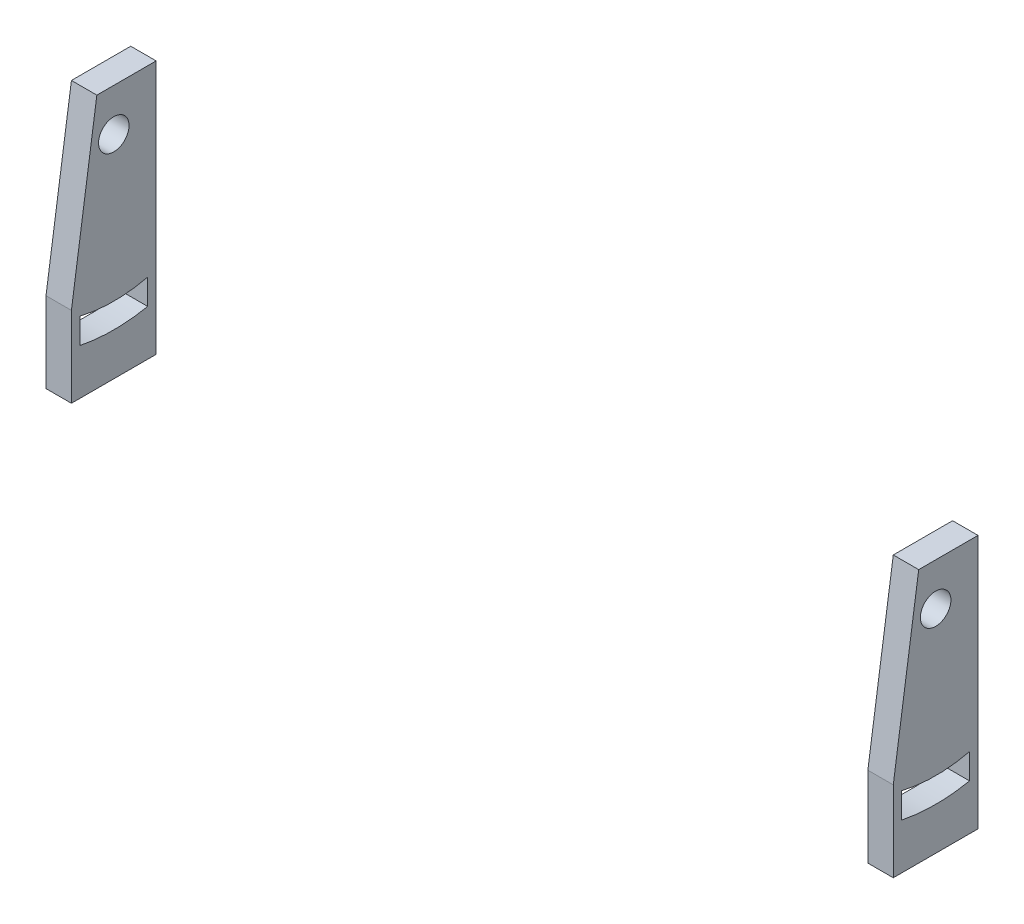
SolidWorks part; units mm, degrees
ref_plane "Front Plane" through (0, 0, 0) normal (0, 0, 1) x (1, 0, 0)
ref_plane "Top Plane" through (0, 0, 0) normal (0, 1, 0) x (1, 0, 0)
ref_plane "Right Plane" through (0, 0, 0) normal (1, 0, 0) x (0, 0, -1)
sketch "Sketch1" plane through (0, 0, 0) normal (1, 0, 0) x (0, 0, -1)
  line L1 (-11.9084, 16.5321) -> (-1.9084, 16.5321)
  line L2 (-11.9084, 16.5321) -> (-11.9084, -13.4679)
  line L3 (-11.9084, -13.4679) -> (-1.9084, -13.4679)
  line L4 (-1.9084, 16.5321) -> (-1.9084, -13.4679)
  dimension "D1" = 30
  dimension "D2" = 10
extrude "Boss-Extrude1" add sketch "Sketch1" along normal blind 100
sketch "Sketch2" plane through (0, 16.5321, 0) normal (0, 1, 0) x (1, 0, 0)
  line L0 (100, -11.9084) -> (0, -11.9084) construction
  line L1 (3, -11.9084) -> (97, -11.9084)
  line L2 (3, -11.9084) -> (3, -1.9084)
  line L3 (3, -1.9084) -> (97, -1.9084)
  line L4 (97, -11.9084) -> (97, -1.9084)
  line L5 (100, -1.9084) -> (0, -1.9084) construction
  dimension "D1" = 3
  dimension "D2" = 3
extrude "Cut-Extrude1" cut sketch "Sketch2" against normal blind 100
sketch "Sketch3" plane through (100, 0, 0) normal (1, 0, 0) x (0, 0, -1)
  line L0 (-1.9084, -13.4679) -> (-1.9084, 16.5321) construction
  line L2 (-11.9084, 16.5321) -> (-11.9084, -13.4679) construction
  line L3 (-1.9084, 16.5321) -> (-11.9084, 16.5321) construction
  circle A0 centre (-6.9084, 11.5321) radius 1.8
  point P4 (-6.9084, 16.5321)
  point P6 (-11.9084, 9.46)
  dimension "D1" = 5
  dimension "D2" = 5
  dimension "D3" = 5
extrude "Cut-Extrude2" cut sketch "Sketch3" against normal blind 100
sketch "Sketch4" plane through (100, 0, 0) normal (1, 0, 0) x (0, 0, -1)
  line L0 (-11.9084, 16.5321) -> (-11.9084, -13.4679) construction
  line L1 (-1.9084, -13.4679) -> (-1.9084, 16.5321) construction
  line L2 (-10.9084, -5.0638) -> (-10.9084, -8.0638)
  line L3 (-2.9109, -5.0644) -> (-2.9084, -8.0638)
  arc A0 (-2.9084, -8.0638) -> (-10.9084, -8.0638) centre (-6.9084, 11.5321) cw
  arc A1 (-2.9109, -5.0644) -> (-10.9084, -5.0638) centre (-6.9084, 11.5321) cw
  dimension "D3" = 20
  dimension "D1" = 1
  dimension "D2" = 1
  dimension "D4" = 1
  dimension "D5" = 1.0024
  dimension "D6" = 3
extrude "Cut-Extrude3" cut sketch "Sketch4" against normal blind 100
sketch "Sketch5" plane through (0, 0, 0) normal (-1, 0, 0) x (0, 0, 1)
  line L0 (8.9084, 16.5321) -> (11.9084, -3.9679)
  line L3 (1.9084, 16.5321) -> (11.9084, 16.5321) construction
  line L4 (11.9084, 16.5321) -> (11.9084, -13.4679) construction
  line L6 (8.9084, 16.5321) -> (11.9084, 16.5321)
  line L9 (11.9084, 16.5321) -> (11.9084, -3.9679)
  dimension "D1" = 3
  dimension "D2" = 9.5
extrude "Cut-Extrude5" cut sketch "Sketch5" against normal blind 100
